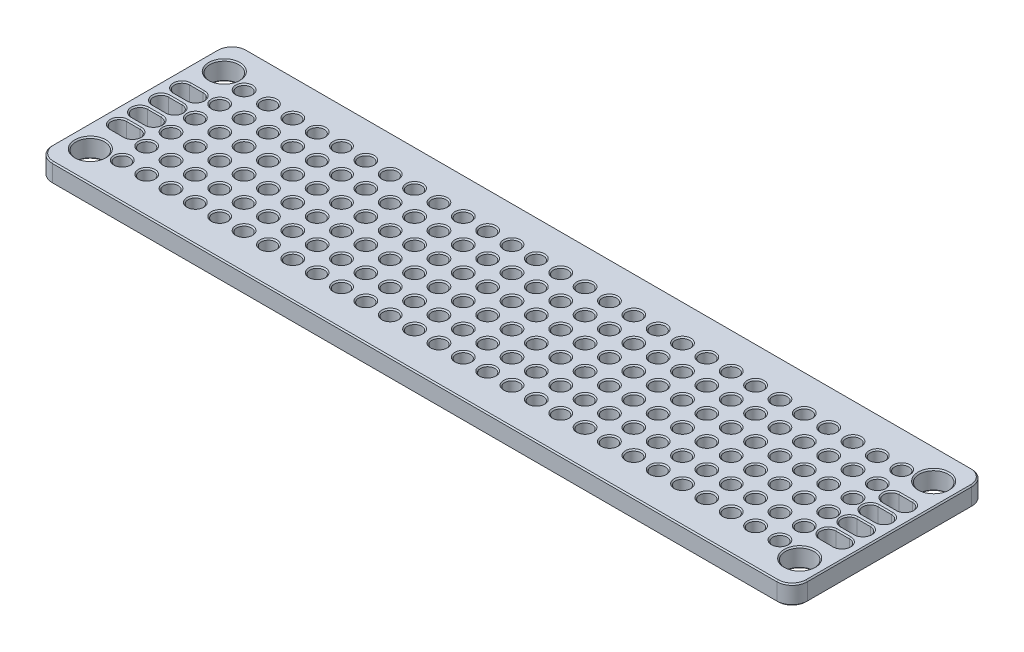
SolidWorks part; units mm, degrees
ref_plane "Front Plane" through (0, 0, 0) normal (0, 0, 1) x (1, 0, 0)
ref_plane "Top Plane" through (0, 0, 0) normal (0, 1, 0) x (1, 0, 0)
ref_plane "Right Plane" through (0, 0, 0) normal (1, 0, 0) x (0, 0, -1)
sketch "Sketch1" plane through (0, 0, 0) normal (0, 1, 0) x (1, 0, 0)
  line L1 (-39.37, -10.16) -> (39.37, -10.16)
  line L2 (-39.37, -10.16) -> (-39.37, 10.16)
  line L3 (-39.37, 10.16) -> (39.37, 10.16)
  line L4 (39.37, -10.16) -> (39.37, 10.16)
  line L5 (-39.37, -10.16) -> (39.37, 10.16) construction
  line L6 (-39.37, 10.16) -> (39.37, -10.16) construction
  point P0 (0, 0)
  dimension "D1" = 78.74
  dimension "D2" = 20.32
extrude "Boss-Extrude1" add sketch "Sketch1" along normal mid plane 1.999 contours L3 L4 L1 L2
sketch "Sketch2" plane through (0, 0, 0) normal (0, 1, 0) x (1, 0, 0)
  line L0 (-36.9888, -6.985) -> (36.9887, -6.985) construction
  line L1 (36.9887, -6.985) -> (36.9887, 6.985) construction
  line L2 (36.9887, 6.985) -> (-36.9888, 6.985) construction
  line L3 (-36.9888, 6.985) -> (-36.9888, -6.985) construction
  line L4 (-36.9888, -6.985) -> (-36.9888, -10.16) construction
  line L5 (-39.37, -10.16) -> (39.37, -10.16) construction
  line L6 (-36.9888, -6.985) -> (-39.37, -6.985) construction
  line L7 (-39.37, -10.16) -> (-39.37, 10.16) construction
  line L8 (36.9887, 6.985) -> (36.9887, 10.16) construction
  line L9 (-39.37, 10.16) -> (39.37, 10.16) construction
  line L10 (36.9887, 6.985) -> (39.37, 6.985) construction
  line L11 (39.37, -10.16) -> (39.37, 10.16) construction
  circle A0 centre (-36.9888, 6.985) radius 1.5
  circle A1 centre (-36.9888, -6.985) radius 1.5
  circle A2 centre (36.9887, -6.985) radius 1.5
  circle A3 centre (36.9887, 6.985) radius 1.5
  dimension "D2" = 3
  dimension "D1" = 3.175
  dimension "D3" = 2.3813
extrude "Cut-Extrude1" cut sketch "Sketch2" against normal through all both and the other way through all contours A0
sketch "Sketch3" plane through (0, 0, 0) normal (0, 1, 0) x (1, 0, 0)
  line L0 (-37.695, 3.291) -> (-36.2825, 3.291) construction
  line L1 (-37.695, 4.0847) -> (-36.2825, 4.0847)
  line L2 (-37.695, 2.4972) -> (-36.2825, 2.4972)
  line L3 (-37.695, 1.097) -> (-36.2825, 1.097) construction
  line L4 (-37.695, 1.8907) -> (-36.2825, 1.8907)
  line L5 (-37.695, 0.3033) -> (-36.2825, 0.3033)
  line L6 (-37.695, -1.097) -> (-36.2825, -1.097) construction
  line L7 (-37.695, -0.3033) -> (-36.2825, -0.3033)
  line L8 (-37.695, -1.8907) -> (-36.2825, -1.8907)
  line L9 (-37.695, -3.291) -> (-36.2825, -3.291) construction
  line L10 (-37.695, -2.4973) -> (-36.2825, -2.4973)
  line L11 (-37.695, -4.0847) -> (-36.2825, -4.0847)
  line L12 (-36.9888, -3.291) -> (-36.9888, -5.485) construction
  line L13 (-36.9888, -3.291) -> (-36.9888, -1.097) construction
  line L14 (-36.9888, -1.097) -> (-36.9888, 1.097) construction
  line L15 (-36.9888, 1.097) -> (-36.9888, 3.291) construction
  line L16 (-36.9888, 3.291) -> (-36.9888, 5.485) construction
  line L17 (-36.9888, -6.985) -> (-36.9888, -5.485) construction
  line L18 (-36.9888, 5.485) -> (-36.9888, 6.985) construction
  line L19 (-35.4888, 6.985) -> (-35.4888, 3.291) construction
  line L20 (0, 10.16) -> (0, -10.16) construction
  line L21 (-39.37, 10.16) -> (39.37, 10.16) construction
  line L22 (-39.37, -10.16) -> (39.37, -10.16) construction
  line L23 (35.4888, 6.985) -> (35.4888, 3.291) construction
  line L24 (36.9888, 5.485) -> (36.9888, 6.985) construction
  line L25 (36.9888, -6.985) -> (36.9888, -5.485) construction
  line L26 (36.9888, 3.291) -> (36.9888, 5.485) construction
  line L27 (36.9888, 1.097) -> (36.9888, 3.291) construction
  line L28 (36.9888, -1.097) -> (36.9888, 1.097) construction
  line L29 (36.9888, -3.291) -> (36.9888, -1.097) construction
  line L30 (36.9888, -3.291) -> (36.9888, -5.485) construction
  line L31 (37.695, -3.291) -> (36.2825, -3.291) construction
  line L32 (37.695, -2.4973) -> (36.2825, -2.4973)
  line L33 (37.695, -4.0847) -> (36.2825, -4.0847)
  line L34 (37.695, -1.097) -> (36.2825, -1.097) construction
  line L35 (37.695, -0.3033) -> (36.2825, -0.3033)
  line L36 (37.695, -1.8907) -> (36.2825, -1.8907)
  line L37 (37.695, 1.097) -> (36.2825, 1.097) construction
  line L38 (37.695, 1.8907) -> (36.2825, 1.8907)
  line L39 (37.695, 0.3033) -> (36.2825, 0.3033)
  line L40 (37.695, 3.291) -> (36.2825, 3.291) construction
  line L41 (37.695, 4.0847) -> (36.2825, 4.0847)
  line L42 (37.695, 2.4972) -> (36.2825, 2.4972)
  arc A0 (-37.695, 4.0847) -> (-37.695, 2.4972) centre (-37.695, 3.291) ccw
  arc A1 (-36.2825, 2.4972) -> (-36.2825, 4.0847) centre (-36.2825, 3.291) ccw
  arc A2 (-37.695, 1.8907) -> (-37.695, 0.3033) centre (-37.695, 1.097) ccw
  arc A3 (-36.2825, 0.3033) -> (-36.2825, 1.8907) centre (-36.2825, 1.097) ccw
  arc A4 (-37.695, -0.3033) -> (-37.695, -1.8907) centre (-37.695, -1.097) ccw
  arc A5 (-36.2825, -1.8907) -> (-36.2825, -0.3033) centre (-36.2825, -1.097) ccw
  arc A6 (-37.695, -2.4973) -> (-37.695, -4.0847) centre (-37.695, -3.291) ccw
  arc A7 (-36.2825, -4.0847) -> (-36.2825, -2.4973) centre (-36.2825, -3.291) ccw
  circle A8 centre (-36.9888, -6.985) radius 1.5 construction
  circle A9 centre (-36.9888, 6.985) radius 1.5 construction
  arc A10 (37.695, -2.4973) -> (37.695, -4.0847) centre (37.695, -3.291) cw
  arc A11 (36.2825, -4.0847) -> (36.2825, -2.4973) centre (36.2825, -3.291) cw
  arc A12 (37.695, -0.3033) -> (37.695, -1.8907) centre (37.695, -1.097) cw
  arc A13 (36.2825, -1.8907) -> (36.2825, -0.3033) centre (36.2825, -1.097) cw
  arc A14 (37.695, 1.8907) -> (37.695, 0.3033) centre (37.695, 1.097) cw
  arc A15 (36.2825, 0.3033) -> (36.2825, 1.8907) centre (36.2825, 1.097) cw
  arc A16 (37.695, 4.0847) -> (37.695, 2.4972) centre (37.695, 3.291) cw
  arc A17 (36.2825, 2.4972) -> (36.2825, 4.0847) centre (36.2825, 3.291) cw
  point P2 (-36.9888, 3.291)
  point P8 (-36.9888, 1.097)
  point P15 (-36.9888, -1.097)
  point P22 (-36.9888, -3.291)
  point P64 (36.9888, -3.291)
  point P71 (36.9888, -1.097)
  point P78 (36.9888, 1.097)
  point P85 (36.9888, 3.291)
  dimension "D1" = 1.5875
extrude "Cut-Extrude2" cut sketch "Sketch3" against normal through all both and the other way through all contours A1 L1 A0 L2
sketch "Sketch4" plane through (0, 0, 0) normal (0, 1, 0) x (1, 0, 0)
  line L0 (-36.9888, 6.985) -> (-36.9888, -6.985) construction
  line L1 (-35.4888, 6.985) -> (-35.4888, -6.985) construction
  line L2 (-34.29, -6.35) -> (-34.29, -3.81) construction
  line L3 (-34.29, -3.81) -> (-34.29, -1.27) construction
  line L4 (-34.29, -1.27) -> (-34.29, 1.27) construction
  line L5 (-34.29, 1.27) -> (-34.29, 3.81) construction
  line L6 (-34.29, 3.81) -> (-34.29, 6.35) construction
  line L7 (-34.29, 6.35) -> (-34.29, 10.16) construction
  line L8 (-39.37, 10.16) -> (39.37, 10.16) construction
  line L9 (-34.29, -6.35) -> (-34.29, -10.16) construction
  line L10 (-39.37, -10.16) -> (39.37, -10.16) construction
  circle A0 centre (-34.29, 6.35) radius 0.7506
  circle A1 centre (-36.9888, 6.985) radius 1.5 construction
  circle A2 centre (-36.9888, -6.985) radius 1.5 construction
  circle A3 centre (-34.29, 3.81) radius 0.7506
  circle A4 centre (-34.29, 1.27) radius 0.7506
  circle A5 centre (-34.29, -1.27) radius 0.7506
  circle A6 centre (-34.29, -3.81) radius 0.7506
  circle A7 centre (-34.29, -6.35) radius 0.7506
  dimension "D1" = 1.5011
  dimension "D3" = 2.54
  dimension "D2" = 2.6987
extrude "Cut-Extrude3" cut sketch "Sketch4" against normal through all both and the other way through all contours A0
pattern_linear "LPattern1" count 28 spacing 2.54 along (1, 0, 0) of "Cut-Extrude3"
fillet "Fillet1" radius 1.5875 4 edges at (-39.37, 0, -10.16) (39.37, 0, -10.16) (39.37, 0, 10.16) (-39.37, 0, 10.16)
chamfer "Chamfer1" distance 0.127 angle 45 400 edges at (34.29, -0.9995, -3.0594) (31.75, -0.9995, -3.0594) (29.21, -0.9995, -3.0594) (26.67, -0.9995, -3.0594) (24.13, -0.9995, -3.0594) (21.59, -0.9995, -3.0594) (19.05, -0.9995, -3.0594) (16.51, -0.9995, -3.0594) (13.97, -0.9995, -3.0594) (11.43, -0.9995, -3.0594) (8.89, -0.9995, -3.0594) (6.35, -0.9995, -3.0594) (3.81, -0.9995, -3.0594) (1.27, -0.9995, -3.0594) (-1.27, -0.9995, -3.0594) (-3.81, -0.9995, -3.0594) (-6.35, -0.9995, -3.0594) (-8.89, -0.9995, -3.0594) (-11.43, -0.9995, -3.0594) (-13.97, -0.9995, -3.0594) (-16.51, -0.9995, -3.0594) (-19.05, -0.9995, -3.0594) (-21.59, -0.9995, -3.0594) (-24.13, -0.9995, -3.0594) (-26.67, -0.9995, -3.0594) (-29.21, -0.9995, -3.0594) (34.29, -0.9995, -0.5194) (31.75, -0.9995, -0.5194) (29.21, -0.9995, -0.5194) (26.67, -0.9995, -0.5194) (24.13, -0.9995, -0.5194) (21.59, -0.9995, -0.5194) (19.05, -0.9995, -0.5194) (16.51, -0.9995, -0.5194) (13.97, -0.9995, -0.5194) (11.43, -0.9995, -0.5194) (8.89, -0.9995, -0.5194) (6.35, -0.9995, -0.5194) (3.81, -0.9995, -0.5194) (1.27, -0.9995, -0.5194) (-1.27, -0.9995, -0.5194) (-3.81, -0.9995, -0.5194) (-6.35, -0.9995, -0.5194) (-8.89, -0.9995, -0.5194) (-11.43, -0.9995, -0.5194) (-13.97, -0.9995, -0.5194) (-16.51, -0.9995, -0.5194) (-19.05, -0.9995, -0.5194) (-21.59, -0.9995, -0.5194) (-24.13, -0.9995, -0.5194) (-26.67, -0.9995, -0.5194) (-29.21, -0.9995, -0.5194) (34.29, -0.9995, 2.0206) (31.75, -0.9995, 2.0206) (29.21, -0.9995, 2.0206) (26.67, -0.9995, 2.0206) (24.13, -0.9995, 2.0206) (21.59, -0.9995, 2.0206) (19.05, -0.9995, 2.0206) (16.51, -0.9995, 2.0206) (13.97, -0.9995, 2.0206) (11.43, -0.9995, 2.0206) (8.89, -0.9995, 2.0206) (6.35, -0.9995, 2.0206) (3.81, -0.9995, 2.0206) (1.27, -0.9995, 2.0206) (-1.27, -0.9995, 2.0206) (-3.81, -0.9995, 2.0206) (-6.35, -0.9995, 2.0206) (-8.89, -0.9995, 2.0206) (-11.43, -0.9995, 2.0206) (-13.97, -0.9995, 2.0206) (-16.51, -0.9995, 2.0206) (-19.05, -0.9995, 2.0206) (-21.59, -0.9995, 2.0206) (-24.13, -0.9995, 2.0206) (-26.67, -0.9995, 2.0206) (-29.21, -0.9995, 2.0206) (34.29, -0.9995, 4.5606) (31.75, -0.9995, 4.5606) (29.21, -0.9995, 4.5606) (26.67, -0.9995, 4.5606) (24.13, -0.9995, 4.5606) (21.59, -0.9995, 4.5606) (19.05, -0.9995, 4.5606) (16.51, -0.9995, 4.5606) (13.97, -0.9995, 4.5606) (11.43, -0.9995, 4.5606) (8.89, -0.9995, 4.5606) (6.35, -0.9995, 4.5606) (3.81, -0.9995, 4.5606) (1.27, -0.9995, 4.5606) (-1.27, -0.9995, 4.5606) (-3.81, -0.9995, 4.5606) (-6.35, -0.9995, 4.5606) (-8.89, -0.9995, 4.5606) (-11.43, -0.9995, 4.5606) (-13.97, -0.9995, 4.5606) (-16.51, -0.9995, 4.5606) (-19.05, -0.9995, 4.5606) (-21.59, -0.9995, 4.5606) (-24.13, -0.9995, 4.5606) (-26.67, -0.9995, 4.5606) (-29.21, -0.9995, 4.5606) (34.29, -0.9995, 7.1006) (31.75, -0.9995, 7.1006) (29.21, -0.9995, 7.1006) (26.67, -0.9995, 7.1006) (24.13, -0.9995, 7.1006) (21.59, -0.9995, 7.1006) (19.05, -0.9995, 7.1006) (16.51, -0.9995, 7.1006) (13.97, -0.9995, 7.1006) (11.43, -0.9995, 7.1006) (8.89, -0.9995, 7.1006) (6.35, -0.9995, 7.1006) (3.81, -0.9995, 7.1006) (1.27, -0.9995, 7.1006) (-1.27, -0.9995, 7.1006) (-3.81, -0.9995, 7.1006) (-6.35, -0.9995, 7.1006) (-8.89, -0.9995, 7.1006) (-11.43, -0.9995, 7.1006) (-13.97, -0.9995, 7.1006) (-16.51, -0.9995, 7.1006) (-19.05, -0.9995, 7.1006) (-21.59, -0.9995, 7.1006) (-24.13, -0.9995, 7.1006) (-26.67, -0.9995, 7.1006) (-29.21, -0.9995, 7.1006) (34.29, -0.9995, -5.5994) (31.75, -0.9995, -5.5994) (29.21, -0.9995, -5.5994) (26.67, -0.9995, -5.5994) (24.13, -0.9995, -5.5994) (21.59, -0.9995, -5.5994) (19.05, -0.9995, -5.5994) (16.51, -0.9995, -5.5994) (13.97, -0.9995, -5.5994) (11.43, -0.9995, -5.5994) (8.89, -0.9995, -5.5994) (6.35, -0.9995, -5.5994) (3.81, -0.9995, -5.5994) (1.27, -0.9995, -5.5994) (-1.27, -0.9995, -5.5994) (-3.81, -0.9995, -5.5994) (-6.35, -0.9995, -5.5994) (-8.89, -0.9995, -5.5994) (-11.43, -0.9995, -5.5994) (-13.97, -0.9995, -5.5994) (-16.51, -0.9995, -5.5994) (-19.05, -0.9995, -5.5994) (-21.59, -0.9995, -5.5994) (-24.13, -0.9995, -5.5994) (-26.67, -0.9995, -5.5994) (-29.21, -0.9995, -5.5994) (-38.905, -0.9995, 9.695) (0, -0.9995, 10.16) (38.905, -0.9995, 9.695) (39.37, -0.9995, 0) (38.905, -0.9995, -9.695) (0, -0.9995, -10.16) (-38.905, -0.9995, -9.695) (-39.37, -0.9995, 0) (-36.9888, -0.9995, -5.485) (-36.9888, -0.9995, 8.485) (36.9887, -0.9995, 8.485) (36.9887, -0.9995, -5.485) (-36.9888, -0.9995, -4.0847) (-35.4888, -0.9995, -3.291) (-36.9888, -0.9995, -2.4972) (-38.4888, -0.9995, -3.291) (36.9888, -0.9995, -2.4972) (35.4888, -0.9995, -3.291) (36.9888, -0.9995, -4.0847) (38.4888, -0.9995, -3.291) (36.9888, -0.9995, -0.3033) (35.4888, -0.9995, -1.097) (36.9888, -0.9995, -1.8907) (38.4888, -0.9995, -1.097) (36.9888, -0.9995, 1.8907) (35.4888, -0.9995, 1.097) (36.9888, -0.9995, 0.3033) (38.4888, -0.9995, 1.097) (36.9888, -0.9995, 4.0847) (35.4888, -0.9995, 3.291) (36.9888, -0.9995, 2.4973) (38.4888, -0.9995, 3.291) (-36.9888, -0.9995, 2.4973) (-35.4888, -0.9995, 3.291) (-36.9888, -0.9995, 4.0847) (-38.4888, -0.9995, 3.291) (-36.9888, -0.9995, 0.3033) (-35.4888, -0.9995, 1.097) (-36.9888, -0.9995, 1.8907) (-38.4888, -0.9995, 1.097) (-36.9888, -0.9995, -1.8907) (-35.4888, -0.9995, -1.097) (-36.9888, -0.9995, -0.3033) (-38.4888, -0.9995, -1.097) (-34.29, -0.9995, 7.1006) (-34.29, -0.9995, 4.5606) (-34.29, -0.9995, 2.0206) (-34.29, -0.9995, -0.5194) (-34.29, -0.9995, -3.0594) (-34.29, -0.9995, -5.5994) (-31.75, -0.9995, -5.5994) (-31.75, -0.9995, 7.1006) (-31.75, -0.9995, 4.5606) (-31.75, -0.9995, 2.0206) (-31.75, -0.9995, -0.5194) (-31.75, -0.9995, -3.0594) (34.29, 0.9995, -3.0594) (31.75, 0.9995, -3.0594) (29.21, 0.9995, -3.0594) (26.67, 0.9995, -3.0594) (24.13, 0.9995, -3.0594) (21.59, 0.9995, -3.0594) (19.05, 0.9995, -3.0594) (16.51, 0.9995, -3.0594) (13.97, 0.9995, -3.0594) (11.43, 0.9995, -3.0594) (8.89, 0.9995, -3.0594) (6.35, 0.9995, -3.0594) (3.81, 0.9995, -3.0594) (1.27, 0.9995, -3.0594) (-1.27, 0.9995, -3.0594) (-3.81, 0.9995, -3.0594) (-6.35, 0.9995, -3.0594) (-8.89, 0.9995, -3.0594) (-11.43, 0.9995, -3.0594) (-13.97, 0.9995, -3.0594) (-16.51, 0.9995, -3.0594) (-19.05, 0.9995, -3.0594) (-21.59, 0.9995, -3.0594) (-24.13, 0.9995, -3.0594) (-26.67, 0.9995, -3.0594) (-29.21, 0.9995, -3.0594) (34.29, 0.9995, -0.5194) (31.75, 0.9995, -0.5194) (29.21, 0.9995, -0.5194) (26.67, 0.9995, -0.5194) (24.13, 0.9995, -0.5194) (21.59, 0.9995, -0.5194) (19.05, 0.9995, -0.5194) (16.51, 0.9995, -0.5194) (13.97, 0.9995, -0.5194) (11.43, 0.9995, -0.5194) (8.89, 0.9995, -0.5194) (6.35, 0.9995, -0.5194) (3.81, 0.9995, -0.5194) (1.27, 0.9995, -0.5194) (-1.27, 0.9995, -0.5194) (-3.81, 0.9995, -0.5194) (-6.35, 0.9995, -0.5194) (-8.89, 0.9995, -0.5194) (-11.43, 0.9995, -0.5194) (-13.97, 0.9995, -0.5194) (-16.51, 0.9995, -0.5194) (-19.05, 0.9995, -0.5194) (-21.59, 0.9995, -0.5194) (-24.13, 0.9995, -0.5194) (-26.67, 0.9995, -0.5194) (-29.21, 0.9995, -0.5194) (34.29, 0.9995, 2.0206) (31.75, 0.9995, 2.0206) (29.21, 0.9995, 2.0206) (26.67, 0.9995, 2.0206) (24.13, 0.9995, 2.0206) (21.59, 0.9995, 2.0206) (19.05, 0.9995, 2.0206) (16.51, 0.9995, 2.0206) (13.97, 0.9995, 2.0206) (11.43, 0.9995, 2.0206) (8.89, 0.9995, 2.0206) (6.35, 0.9995, 2.0206) (3.81, 0.9995, 2.0206) (1.27, 0.9995, 2.0206) (-1.27, 0.9995, 2.0206) (-3.81, 0.9995, 2.0206) (-6.35, 0.9995, 2.0206) (-8.89, 0.9995, 2.0206) (-11.43, 0.9995, 2.0206) (-13.97, 0.9995, 2.0206) (-16.51, 0.9995, 2.0206) (-19.05, 0.9995, 2.0206) (-21.59, 0.9995, 2.0206) (-24.13, 0.9995, 2.0206) (-26.67, 0.9995, 2.0206) (-29.21, 0.9995, 2.0206) (34.29, 0.9995, 4.5606) (31.75, 0.9995, 4.5606) (29.21, 0.9995, 4.5606) (26.67, 0.9995, 4.5606) (24.13, 0.9995, 4.5606) (21.59, 0.9995, 4.5606) (19.05, 0.9995, 4.5606) (16.51, 0.9995, 4.5606) (13.97, 0.9995, 4.5606) (11.43, 0.9995, 4.5606) (8.89, 0.9995, 4.5606) (6.35, 0.9995, 4.5606) (3.81, 0.9995, 4.5606) (1.27, 0.9995, 4.5606) (-1.27, 0.9995, 4.5606) (-3.81, 0.9995, 4.5606) (-6.35, 0.9995, 4.5606) (-8.89, 0.9995, 4.5606) (-11.43, 0.9995, 4.5606) (-13.97, 0.9995, 4.5606) (-16.51, 0.9995, 4.5606) (-19.05, 0.9995, 4.5606) (-21.59, 0.9995, 4.5606) (-24.13, 0.9995, 4.5606) (-26.67, 0.9995, 4.5606) (-29.21, 0.9995, 4.5606) (34.29, 0.9995, 7.1006) (31.75, 0.9995, 7.1006) (29.21, 0.9995, 7.1006) (26.67, 0.9995, 7.1006) (24.13, 0.9995, 7.1006) (21.59, 0.9995, 7.1006) (19.05, 0.9995, 7.1006) (16.51, 0.9995, 7.1006) (13.97, 0.9995, 7.1006) (11.43, 0.9995, 7.1006) (8.89, 0.9995, 7.1006) (6.35, 0.9995, 7.1006) (3.81, 0.9995, 7.1006) (1.27, 0.9995, 7.1006) (-1.27, 0.9995, 7.1006) (-3.81, 0.9995, 7.1006) (-6.35, 0.9995, 7.1006) (-8.89, 0.9995, 7.1006) (-11.43, 0.9995, 7.1006) (-13.97, 0.9995, 7.1006) (-16.51, 0.9995, 7.1006) (-19.05, 0.9995, 7.1006) (-21.59, 0.9995, 7.1006) (-24.13, 0.9995, 7.1006) (-26.67, 0.9995, 7.1006) (-29.21, 0.9995, 7.1006) (34.29, 0.9995, -5.5994) (31.75, 0.9995, -5.5994) (29.21, 0.9995, -5.5994) (26.67, 0.9995, -5.5994) (24.13, 0.9995, -5.5994) (21.59, 0.9995, -5.5994) (19.05, 0.9995, -5.5994) (16.51, 0.9995, -5.5994) (13.97, 0.9995, -5.5994) (11.43, 0.9995, -5.5994) (8.89, 0.9995, -5.5994) (6.35, 0.9995, -5.5994) (3.81, 0.9995, -5.5994) (1.27, 0.9995, -5.5994) (-1.27, 0.9995, -5.5994) (-3.81, 0.9995, -5.5994) (-6.35, 0.9995, -5.5994) (-8.89, 0.9995, -5.5994) (-11.43, 0.9995, -5.5994) (-13.97, 0.9995, -5.5994) (-16.51, 0.9995, -5.5994) (-19.05, 0.9995, -5.5994) (-21.59, 0.9995, -5.5994) (-24.13, 0.9995, -5.5994) (-26.67, 0.9995, -5.5994) (-29.21, 0.9995, -5.5994) (38.905, 0.9995, -9.695) (39.37, 0.9995, 0) (38.905, 0.9995, 9.695) (0, 0.9995, 10.16) (-38.905, 0.9995, 9.695) (-39.37, 0.9995, 0) (-38.905, 0.9995, -9.695) (0, 0.9995, -10.16) (-36.9888, 0.9995, -5.485) (-36.9888, 0.9995, 8.485) (36.9887, 0.9995, 8.485) (36.9887, 0.9995, -5.485) (-35.4888, 0.9995, -3.291) (-36.9888, 0.9995, -4.0847) (-38.4888, 0.9995, -3.291) (-36.9888, 0.9995, -2.4972) (35.4888, 0.9995, -3.291) (36.9888, 0.9995, -2.4972) (38.4888, 0.9995, -3.291) (36.9888, 0.9995, -4.0847) (35.4888, 0.9995, -1.097) (36.9888, 0.9995, -0.3033) (38.4888, 0.9995, -1.097) (36.9888, 0.9995, -1.8907) (35.4888, 0.9995, 1.097) (36.9888, 0.9995, 1.8907) (38.4888, 0.9995, 1.097) (36.9888, 0.9995, 0.3033) (35.4888, 0.9995, 3.291) (36.9888, 0.9995, 4.0847) (38.4888, 0.9995, 3.291) (36.9888, 0.9995, 2.4973)
